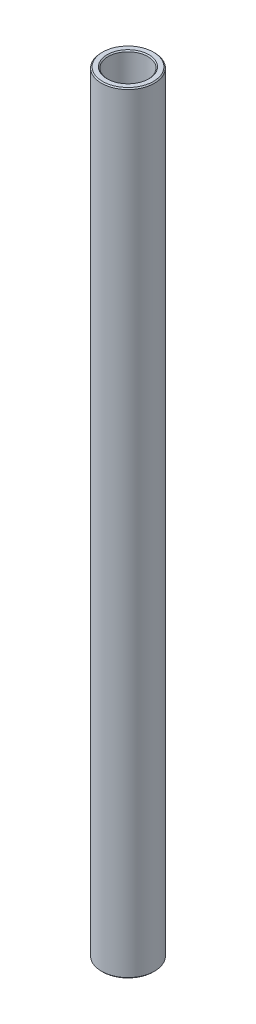
SolidWorks part; units mm, degrees
ref_plane "Front Plane" through (0, 0, 0) normal (0, 0, 1) x (1, 0, 0)
ref_plane "Top Plane" through (0, 0, 0) normal (0, 1, 0) x (1, 0, 0)
ref_plane "Right Plane" through (0, 0, 0) normal (1, 0, 0) x (0, 0, -1)
sketch "Sketch1" plane through (0, 0, 0) normal (0, 0, 1) x (1, 0, 0)
  line L0 (0, 11.6086) -> (0, -11.6086) construction
  line L1 (4.7625, 92.4719) -> (6.35, 92.4719)
  line L2 (6.35, 92.4719) -> (6.35, -92.4719)
  line L3 (6.35, -92.4719) -> (4.7625, -92.4719)
  line L4 (4.7625, -92.4719) -> (4.7625, 92.4719)
  line L5 (4.7625, 0) -> (0, 0) construction
  dimension "D1" = 9.525
  dimension "D2" = 12.7
  dimension "D3" = 184.9437
revolve "Revolve1" add sketch "Sketch1" angle 360 about L0
chamfer "Chamfer1" distance 0.254 angle 45 4 edges at (-4.7625, -92.4719, 0) (-6.35, -92.4719, 0) (-6.35, 92.4719, 0) (-4.7625, 92.4719, 0)
